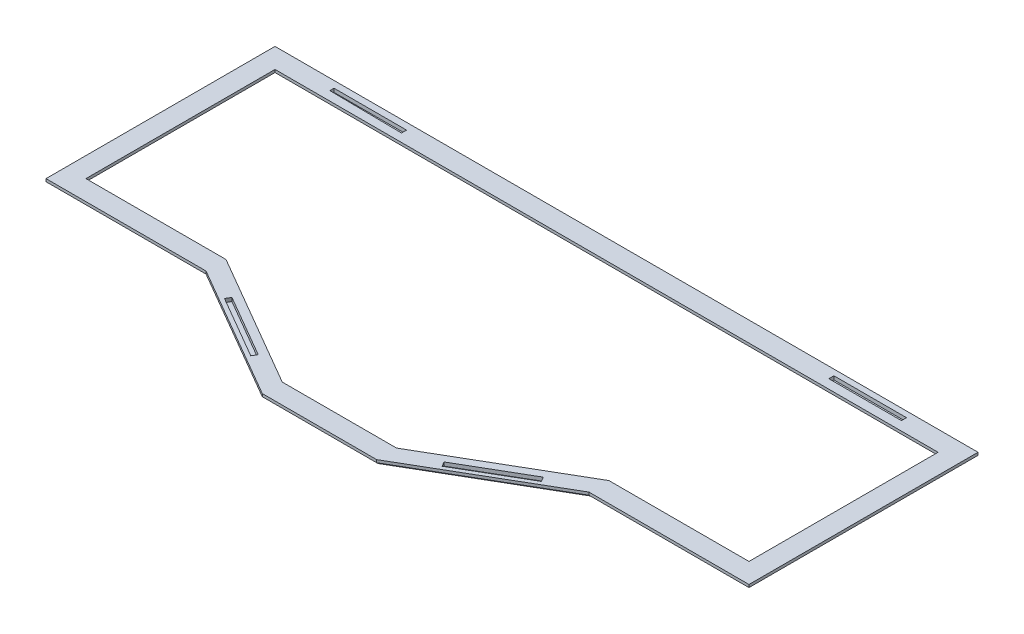
SolidWorks part; units mm, degrees
ref_plane "Front Plane" through (0, 0, 0) normal (0, 0, 1) x (1, 0, 0)
ref_plane "Top Plane" through (0, 0, 0) normal (0, 1, 0) x (1, 0, 0)
ref_plane "Right Plane" through (0, 0, 0) normal (1, 0, 0) x (0, 0, -1)
sketch "Sketch1" plane through (0, 0, 0) normal (0, 1, 0) x (1, 0, 0)
  line L1 (-193.7, 84.7) -> (193.7, 84.7)
  line L2 (-193.7, 84.7) -> (-193.7, -84.7)
  line L3 (-193.7, -84.7) -> (193.7, -84.7)
  line L4 (193.7, 84.7) -> (193.7, -84.7)
  line L5 (-193.7, 84.7) -> (193.7, -84.7) construction
  line L6 (-193.7, -84.7) -> (193.7, 84.7) construction
  point P0 (0, 0)
  dimension "D1" = 387.4
  dimension "D2" = 169.4
extrude "Boss-Extrude1" add sketch "Sketch1" along normal blind 2.5
sketch "Sketch3" plane through (0, 2.5, 0) normal (0, 1, 0) x (1, 0, 0)
  line L0 (193.7, 84.7) -> (157.5, 84.7) construction
  line L1 (193.7, 84.7) -> (-193.7, 84.7) construction
  line L2 (157.5, 81.5) -> (157.5, 78.7)
  line L4 (157.5, 78.7) -> (117.5, 78.7)
  line L6 (117.5, 78.7) -> (117.5, 81.5)
  line L7 (117.5, 81.5) -> (157.5, 81.5)
  line L8 (157.5, 84.7) -> (157.5, 78.7) construction
  line L9 (-193.7, 84.7) -> (-157.5, 84.7) construction
  line L10 (-157.5, 81) -> (-157.5, 78.7)
  line L11 (-157.5, 78.7) -> (-117.5, 78.2)
  line L12 (-117.5, 78.2) -> (-117.5, 81)
  line L13 (-117.5, 81) -> (-157.5, 81)
  line L14 (-157.5, 84.7) -> (-157.5, 78.7) construction
  point P7 (0, 0)
  dimension "D1" = 36.2
  dimension "D2" = 2.8
  dimension "D3" = 40
  dimension "D4" = 36.2
  dimension "D5" = 2.8
  dimension "D6" = 40
  dimension "D7" = 6
  dimension "D8" = 6
extrude "Cut-Extrude2" cut sketch "Sketch3" against normal blind 2
sketch "Sketch4" plane through (0, 0, 0) normal (0, -1, 0) x (1, 0, 0)
  line L0 (31.5, 73.5) -> (105.5, 30.5)
  line L1 (105.5, 30.5) -> (182.7, 30.5)
  line L2 (182.7, 30.5) -> (182.7, -73.7)
  line L3 (182.7, -73.7) -> (-182.7, -73.7)
  line L4 (-182.7, -73.7) -> (-182.7, 30.5)
  line L5 (-182.7, 30.5) -> (-105.5, 30.5)
  line L6 (-105.5, 30.5) -> (-31.5, 73.5)
  line L7 (-31.5, 73.5) -> (31.5, 73.5)
  line L8 (-144.1, 30.5) -> (-144.1, 84.7) construction
  line L9 (-193.7, 84.7) -> (193.7, 84.7) construction
  line L10 (0, 73.5) -> (0, 84.7) construction
  line L11 (144.1, 30.5) -> (144.1, 84.7) construction
  line L12 (0, -73.7) -> (0, -84.7) construction
  line L13 (193.7, -84.7) -> (-193.7, -84.7) construction
  line L14 (-182.7, -21.6) -> (-193.7, -21.6) construction
  line L15 (-193.7, -84.7) -> (-193.7, 84.7) construction
  line L16 (182.7, -21.6) -> (193.7, -21.6) construction
  line L17 (193.7, 84.7) -> (193.7, -84.7) construction
  line L18 (-105.5, 30.5) -> (-105.5, 35.5) construction
  line L19 (105.5, 30.5) -> (105.5, 35.5) construction
  dimension "D1" = 54.2
  dimension "D2" = 11.2
  dimension "D3" = 11
  dimension "D4" = 11
extrude "Cut-Extrude3" cut sketch "Sketch4" against normal blind 10
sketch "Sketch7" plane through (0, 0, 0) normal (0, -1, 0) x (1, 0, 0)
  line L0 (193.7, 41.5) -> (105.5, 41.5)
  line L1 (193.7, 84.7) -> (193.7, -84.7) construction
  line L2 (105.5, 41.5) -> (31.5, 84.5)
  line L3 (31.5, 84.5) -> (-31.5, 84.5)
  line L4 (-31.5, 84.5) -> (-105.5, 41.5)
  line L5 (-105.5, 41.5) -> (-193.7, 41.5)
  line L6 (-193.7, -84.7) -> (-193.7, 84.7) construction
  line L7 (-144.1, 30.5) -> (-144.1, 41.5) construction
  line L8 (-105.5, 30.5) -> (-182.7, 30.5) construction
  line L9 (-105.5, 30.5) -> (-105.5, 41.5) construction
  line L10 (105.5, 30.5) -> (105.5, 41.5) construction
  line L11 (144.1, 30.5) -> (144.1, 41.5) construction
  line L12 (182.7, 30.5) -> (105.5, 30.5) construction
  line L13 (0, 73.5) -> (0, 84.5) construction
  line L14 (31.5, 73.5) -> (-31.5, 73.5) construction
  line L15 (-31.5, 73.5) -> (-31.5, 84.5) construction
  line L16 (31.5, 73.5) -> (31.5, 84.5) construction
  line L17 (-193.7, 41.5) -> (-193.7, 84.7)
  line L18 (-193.7, 84.7) -> (193.7, 84.7)
  line L19 (193.7, 84.7) -> (193.7, 41.5)
  dimension "D3" = 11
  dimension "D1" = 11
  dimension "D2" = 11
extrude "Cut-Extrude4" cut sketch "Sketch7" against normal through all
chamfer "Chamfer1" distance 1 angle 45 8 edges at (-68.5, 0, 63) (-149.6, 0, 41.5) (-193.7, 0, -21.6) (0, 0, -84.7) (193.7, 0, -21.6) (149.6, 0, 41.5) (68.5, 0, 63) (0, 0, 84.5)
chamfer "Chamfer2" distance 1 angle 45 8 edges at (-68.5, 0, 52) (-144.1, 0, 30.5) (-182.7, 0, -21.6) (0, 0, -73.7) (182.7, 0, -21.6) (144.1, 0, 30.5) (68.5, 0, 52) (0, 0, 73.5)
sketch "Sketch9" plane through (0, 2.5, 0) normal (0, 1, 0) x (1, 0, 0)
  line L0 (-70.0073, -59.5939) -> (-52.7147, -69.6422)
  line L1 (-52.7147, -69.6422) -> (-87.2998, -49.5455) construction
  line L2 (-52.7147, -69.6422) -> (-51.2075, -67.0483)
  line L3 (-51.2075, -67.0483) -> (-85.7925, -46.9517)
  line L4 (-85.7925, -46.9517) -> (-87.2998, -49.5455)
  line L5 (-87.2998, -49.5455) -> (-70.0073, -59.5939)
  line L6 (70.0073, -59.5939) -> (52.7147, -69.6422)
  line L7 (87.2998, -49.5455) -> (52.7147, -69.6422) construction
  line L8 (52.7147, -69.6422) -> (51.2075, -67.0483)
  line L9 (51.2075, -67.0483) -> (85.7925, -46.9517)
  line L10 (85.7925, -46.9517) -> (87.2998, -49.5455)
  line L11 (87.2998, -49.5455) -> (70.0073, -59.5939)
  point P5 (0, 0)
  point P23 (0, 0)
  point P24 (0, 0)
  point P25 (0, 0)
  dimension "D3" = 40
  dimension "D1" = 40
  dimension "D2" = 3
  dimension "D4" = 3
extrude "Cut-Extrude5" cut sketch "Sketch9" against normal blind 2
equation "\"full_width\"=375"
equation "\"D1@Sketch1\"=\"full_width\"+(\"added_width\"*2)+(\"margin1\"*2)"
equation "\"added_width\"=6"
equation "\"full_height\"= 157"
equation "\"D2@Sketch1\"=\"full_height\"+(\"added_height\"*2)+(\"margin1\"*2)"
equation "\"added_height\"=6"
equation "\"D1@Sketch3\"=30.00mm+\"added_width\"+\"margin1\""
equation "\"tab_depth\" = 3"
equation "\"D2@Sketch3\"=\"tab_depth\"-\"margin1\""
equation "\"tab_width\"= 40"
equation "\"D3@Sketch3\"=\"tab_width\""
equation "\"tab_height\"=2"
equation "\"D1@Cut-Extrude2\"=\"tab_height\""
equation "\"D4@Sketch3\"=30mm+\"added_width\"+\"margin1\""
equation "\"D5@Sketch3\"=\"tab_depth\"-\"margin1\""
equation "\"D6@Sketch3\"=\"tab_width\""
equation "\"margin1\"= 0.2"
equation "\"angle_dist\"=32.037"
equation "\"chin_dist\"=6.2"
equation "\"D2@Sketch4\"=\"chin_dist\"+5"
equation "\"flat_dist\"=49.2"
equation "\"D1@Sketch4\"=\"flat_dist\"+5"
equation "\"D3@Sketch4\"=\"added_height\"+5"
equation "\"D4@Sketch4\"=\"added_width\"+5"
equation "\"D7@Sketch3\"=\"added_height\""
equation "\"D8@Sketch3\"=\"added_height\""
equation "\"width1\"= 11"
equation "\"D3@Sketch7\"=\"width1\""
equation "\"D2@Sketch7\"=\"width1\""
equation "\"D1@Sketch7\"=\"width1\""
equation "\"D1@Sketch9\"=\"tab_width\""
equation "\"D2@Sketch9\"=\"tab_depth\""
equation "\"D3@Sketch9\"=\"tab_width\""
equation "\"D4@Sketch9\"=\"tab_depth\""
equation "\"D1@Cut-Extrude5\"=\"tab_height\""
